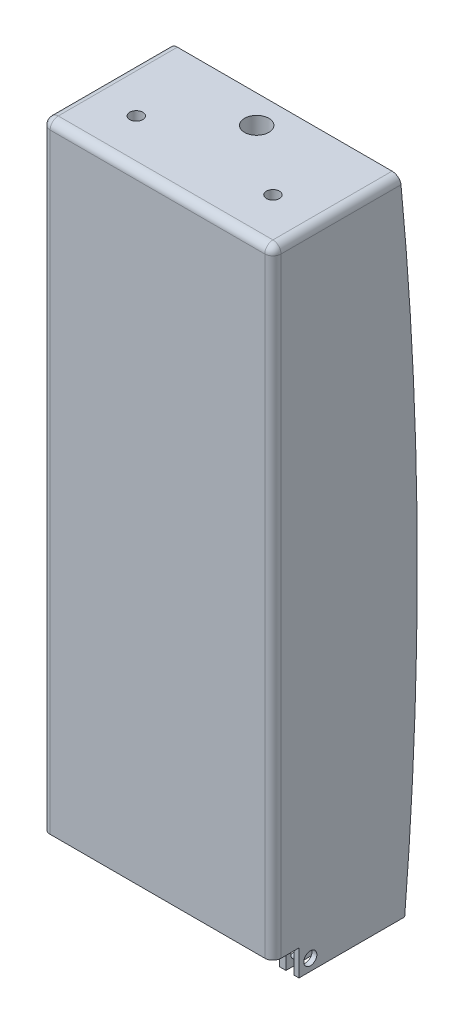
SolidWorks part; units mm, degrees
ref_plane "Front Plane" through (0, 0, 0) normal (0, 0, 1) x (1, 0, 0)
ref_plane "Top Plane" through (0, 0, 0) normal (0, 1, 0) x (1, 0, 0)
ref_plane "Right Plane" through (0, 0, 0) normal (1, 0, 0) x (0, 0, -1)
sketch "Sketch4" plane through (0, 0, 0) normal (0, 0, 1) x (1, 0, 0)
  line L0 (-65, 400) -> (-65, 10)
  line L1 (-55, 0) -> (55, 0)
  line L2 (65, 10) -> (65, 400)
  line L3 (65, 400) -> (-65, 400)
  line L4 (0, 0) -> (0, 180.0439) construction
  arc A0 (-55, 0) -> (-65, 10) centre (-55, 10) cw
  arc A1 (55, 0) -> (65, 10) centre (55, 10) ccw
  point P6 (-65, 0)
  dimension "D3" = 10
  dimension "D4" = 10
  dimension "D1" = 130
  dimension "D2" = 400
  dimension "D5" = 0
  dimension "D6" = 65
sketch "Sketch6" plane through (0, 0, 0) normal (1, 0, 0) x (0, 0, -1)
  line L0 (0, 10) -> (0, 400) construction
  line L1 (45, 406) -> (-45, 406)
  line L2 (45, 406) -> (45, 394)
  line L3 (45, 394) -> (-45, 394)
  line L4 (-45, 406) -> (-45, 394)
  line L5 (45, 406) -> (-45, 394) construction
  line L6 (45, 394) -> (-45, 406) construction
  point P0 (0, 400)
  dimension "D1" = 90
  dimension "D2" = 12
  dimension "D3" = 400
sweep "Sweep2" add profiles "Sketch6" path "Sketch4"
sketch "Sketch7" plane through (0, 0, 0) normal (0, 1, 0) x (1, 0, 0)
  line L1 (-80.8354, -49.7013) -> (80.8354, -49.7013)
  line L2 (-80.8354, -49.7013) -> (-80.8354, 49.7013)
  line L3 (-80.8354, 49.7013) -> (80.8354, 49.7013)
  line L4 (80.8354, -49.7013) -> (80.8354, 49.7013)
  line L5 (-80.8354, -49.7013) -> (80.8354, 49.7013) construction
  line L6 (-80.8354, 49.7013) -> (80.8354, -49.7013) construction
  point P0 (0, 0)
extrude "Cut-Extrude1" cut sketch "Sketch7" against normal blind 10 and the other way blind 10
sketch "Sketch8" plane through (0, 0, 0) normal (0, 1, 0) x (1, 0, 0)
  line L0 (0, -45) -> (0, 45) construction
  line L1 (-68, -46.7578) -> (-63, -46.7578)
  line L2 (-68, -46.7578) -> (-68, 47.2422)
  line L3 (-68, 47.2422) -> (-63, 47.2422)
  line L4 (-63, -46.7578) -> (-63, 47.2422)
  line L5 (-68, -46.7578) -> (-63, 47.2422) construction
  line L6 (-68, 47.2422) -> (-63, -46.7578) construction
  line L7 (68, 47.2422) -> (63, 47.2422)
  line L8 (63, -46.7578) -> (63, 47.2422)
  line L9 (68, -46.7578) -> (63, -46.7578)
  line L10 (68, -46.7578) -> (68, 47.2422)
  point P0 (-65.5, 0.2422)
  dimension "D1" = 5
  dimension "D2" = 63
  dimension "D3" = 94
extrude "Cut-Extrude2" cut sketch "Sketch8" along normal blind 35
sketch "Sketch9" plane through (0, 406, 0) normal (0, 1, 0) x (1, 0, 0)
  line L0 (0, 0) -> (-71, 0) construction
  line L1 (-71, -45) -> (-71, 45) construction
  line L2 (0, 45) -> (0, -45) construction
  circle A0 centre (0, 0) radius 7.5
  circle A1 centre (-42, 32) radius 4
  circle A2 centre (-42, -32) radius 4
  circle A3 centre (42, -32) radius 4
  circle A4 centre (42, 32) radius 4
  dimension "D1" = 15
  dimension "D2" = 8
  dimension "D3" = 8
  dimension "D4" = 32
  dimension "D5" = 32
  dimension "D6" = 42
  dimension "D7" = 42
extrude "Cut-Extrude3" cut sketch "Sketch9" against normal through all
sketch "Sketch10" plane through (71, 0, 0) normal (1, 0, 0) x (0, 0, -1)
  line L0 (45, 10) -> (-45, 10) construction
  line L1 (-45, 406) -> (-45, 10) construction
  circle A0 centre (-38, 17) radius 4
  dimension "D1" = 8
  dimension "D2" = 7
  dimension "D3" = 7
extrude "Cut-Extrude4" cut sketch "Sketch10" against normal through all
sketch "Sketch11" plane through (0, 406, 0) normal (0, 1, 0) x (1, 0, 0)
  line L1 (-71, -61) -> (71, -61)
  line L2 (-71, -61) -> (-71, -45)
  line L3 (-71, -45) -> (71, -45)
  line L4 (71, -61) -> (71, -45)
  line L5 (-71, -61) -> (71, -45) construction
  line L6 (-71, -45) -> (71, -61) construction
  point P0 (0, -53)
  dimension "D1" = 142
  dimension "D2" = 16
extrude "Boss-Extrude1" add sketch "Sketch11" against normal blind 380
fillet "Fillet2" radius 5 3 edges at (63, 22.5, -45) (61, 10, -45) (59, 202, -45)
fillet "Fillet3" radius 5 3 edges at (68, 22.5, -45) (71, 208, -45) (69.5, 10, -45)
fillet "Fillet4" radius 5 3 edges at (-61, 10, -45) (-59, 202, -45) (-63, 22.5, -45)
fillet "Fillet5" radius 5 3 edges at (-69.5, 10, -45) (-68, 22.5, -45) (-71, 208, -45)
fillet "Fillet6" radius 5 13 edges at (71, 216, 61) (-71, 216, 61) (0, 406, 61) (71, 403.5, -40) (66, 403.5, -45) (69.5355, 406, -43.5355) (-71, 403.5, -40) (-33, 406, -45) (-66, 403.5, -45) (-69.5355, 406, -43.5355) (33, 406, -45) (71, 406, 10.5) (-71, 406, 10.5)
sketch "Sketch12" plane through (-71, 0, 0) normal (-1, 0, 0) x (0, 0, 1)
  line L0 (-19.9981, 10) -> (-79.773, 10)
  line L1 (-40, 10) -> (45, 10) construction
  line L2 (-79.773, 10) -> (-79.773, 406.4421)
  line L3 (-79.773, 406.4421) -> (-17.2492, 406)
  line L4 (-40, 406) -> (56, 406) construction
  arc A0 (-19.9981, 10) -> (-17.2492, 406) centre (2142.2718, 193) cw
  dimension "D1" = 2170
  dimension "D2" = 59.7749
extrude "Cut-Extrude5" cut sketch "Sketch12" against normal through all
